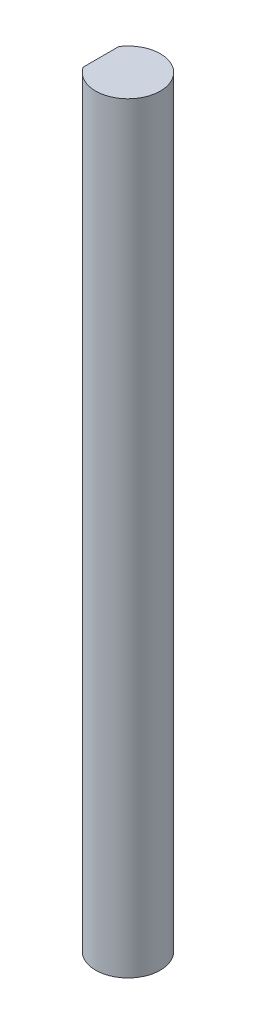
SolidWorks part; units mm, degrees
ref_plane "Front Plane" through (0, 0, 0) normal (0, 0, 1) x (1, 0, 0)
ref_plane "Top Plane" through (0, 0, 0) normal (0, 1, 0) x (1, 0, 0)
ref_plane "Right Plane" through (0, 0, 0) normal (1, 0, 0) x (0, 0, -1)
sketch "Sketch1" plane through (0, 0, 0) normal (0, 1, 0) x (1, 0, 0)
  line L0 (-1.25, -0.8292) -> (-1.25, 0.8292)
  arc A0 (-1.25, -0.8292) -> (-1.25, 0.8292) centre (0, 0) ccw
  dimension "D1" = 1.25
  dimension "D2" = 3
extrude "Boss-Extrude1" add sketch "Sketch1" along normal blind 35.3
